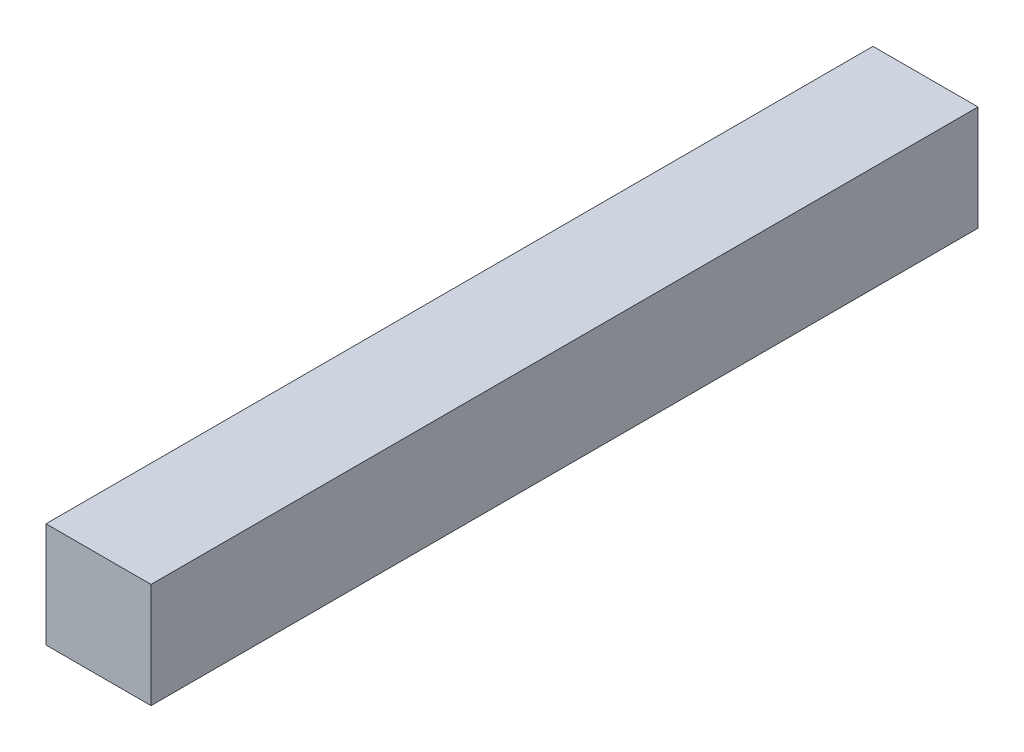
SolidWorks part; units mm, degrees
ref_plane "Front Plane" through (0, 0, 0) normal (0, 0, 1) x (1, 0, 0)
ref_plane "Top Plane" through (0, 0, 0) normal (0, 1, 0) x (1, 0, 0)
ref_plane "Right Plane" through (0, 0, 0) normal (1, 0, 0) x (0, 0, -1)
sketch "Sketch1" plane through (0, 0, 0) normal (0, 0, 1) x (1, 0, 0)
  line L1 (-1.5875, -1.5875) -> (1.5875, -1.5875)
  line L2 (-1.5875, -1.5875) -> (-1.5875, 1.5875)
  line L3 (-1.5875, 1.5875) -> (1.5875, 1.5875)
  line L4 (1.5875, -1.5875) -> (1.5875, 1.5875)
  line L5 (-1.5875, -1.5875) -> (1.5875, 1.5875) construction
  line L6 (-1.5875, 1.5875) -> (1.5875, -1.5875) construction
  point P0 (0, 0)
extrude "Boss-Extrude1" add sketch "Sketch1" along normal blind 25
